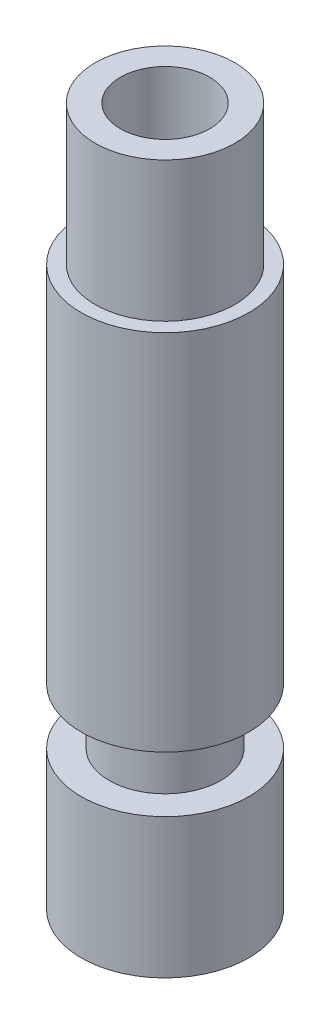
SolidWorks part; units mm, degrees
ref_plane "Front Plane" through (0, 0, 0) normal (0, 0, 1) x (1, 0, 0)
ref_plane "Top Plane" through (0, 0, 0) normal (0, 1, 0) x (1, 0, 0)
ref_plane "Right Plane" through (0, 0, 0) normal (1, 0, 0) x (0, 0, -1)
sketch "Sketch1" plane through (0, 0, 0) normal (0, 0, 1) x (1, 0, 0)
  line L0 (0, 0) -> (0, 25)
  line L1 (0, 25) -> (2.5, 25)
  line L2 (2.5, 25) -> (2.5, 20)
  line L3 (2.5, 20) -> (3, 20)
  line L4 (3, 20) -> (3, 7)
  line L5 (3, 7) -> (2, 7)
  line L6 (2, 7) -> (2, 5)
  line L7 (2, 5) -> (3, 5)
  line L8 (3, 5) -> (3, 0)
  line L9 (3, 0) -> (0, 0)
  dimension "D1" = 3
  dimension "D2" = 2
  dimension "D3" = 3
  dimension "D4" = 2.5
  dimension "D5" = 7
  dimension "D6" = 2
  dimension "D7" = 18
  dimension "D8" = 5
revolve "Revolve1" add sketch "Sketch1" angle 360 about L0
sketch "Sketch2" plane through (0, 25, 0) normal (0, 1, 0) x (1, 0, 0)
  circle A0 centre (0, 0) radius 1.6
  dimension "D1" = 3.2
extrude "Cut-Extrude1" cut sketch "Sketch2" against normal through all
